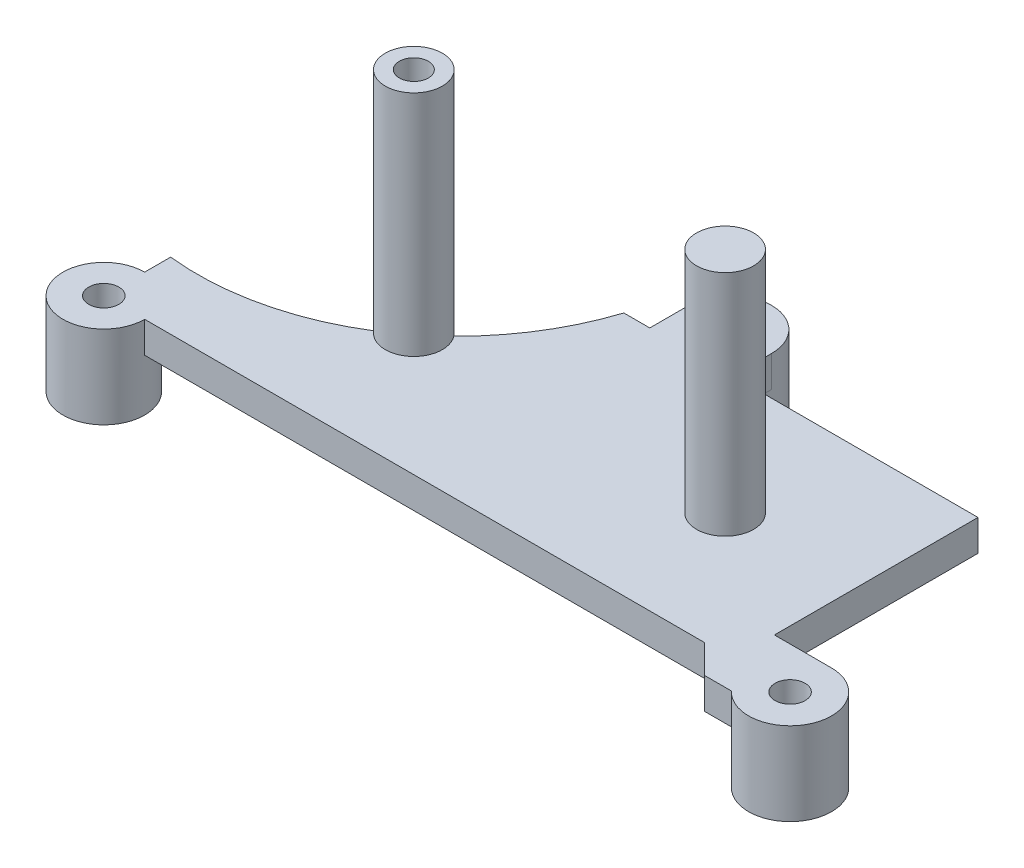
SolidWorks part; units mm, degrees
ref_plane "Front Plane" through (0, 0, 0) normal (0, 0, 1) x (1, 0, 0)
ref_plane "Top Plane" through (0, 0, 0) normal (0, 1, 0) x (1, 0, 0)
ref_plane "Right Plane" through (0, 0, 0) normal (1, 0, 0) x (0, 0, -1)
sketch "Sketch1" plane through (0, 0, 0) normal (0, 1, 0) x (1, 0, 0)
  line L0 (38.5, -3.4862) -> (35.0138, 0)
  line L1 (-38.5, 29.9974) -> (38.5, 29.9974)
  line L2 (-38.5, 29.9974) -> (-38.5, 0)
  line L3 (-38.5, 0) -> (38.5, 0)
  line L4 (38.5, 29.9974) -> (38.5, 0)
  line L5 (-1.6701, 29.9974) -> (8.49, 29.9974)
  line L6 (-1.6701, 29.9974) -> (-1.6701, 34.7599)
  line L7 (-1.6701, 34.7599) -> (8.4899, 34.7599)
  line L8 (8.49, 29.9974) -> (8.4899, 34.7599)
  line L9 (38.5001, 5.08) -> (45.4978, 5.08)
  line L10 (38.5001, 5.08) -> (38.5, -3.4862)
  line L11 (38.5, -3.4862) -> (45.4978, -3.4862)
  line L12 (45.4978, 5.08) -> (45.4978, -3.4862)
  circle A0 centre (-38.5, 0) radius 1.8415
  circle A1 centre (3.4099, 34.7599) radius 1.8415
  circle A2 centre (45.4978, 0) radius 1.8415
  circle A3 centre (-38.5, 0) radius 5.002
  arc A5 (-1.6701, 34.7599) -> (8.4899, 34.7599) centre (3.4099, 34.7599) cw
  circle A6 centre (45.4978, 0) radius 5.08
  dimension "D4" = 3.683
  dimension "D5" = 3.683
  dimension "D3" = 3.683
  dimension "D9" = 10.16
  dimension "D11" = 41.91
  dimension "D1" = 77.0001
  dimension "D2" = 29.9974
  dimension "D6" = 4.7625
  dimension "D7" = 83.9978
  dimension "D8" = 10.16
  dimension "D10" = 6.9977
extrude "Boss-Extrude1" add sketch "Sketch1" along normal blind 3.81 contours A3 L3 L4 L1 L2 | L3 A3 L2 A0 | L2 A3 L3 A0 | L12 A6 L11 A2 | A6 L9 L4 L10 L11 | L11 A6 L12 A2 | A5 L7 A1 | A1 L7 L6 L1 L8 | L10 L3 L0
sketch "Sketch2" plane through (0, 0, 0) normal (0, 1, 0) x (1, 0, 0)
  line L0 (-38.5, 29.9974) -> (-1.6701, 29.9974) construction
  line L2 (-38.5, 29.9974) -> (-38.5, 5.002) construction
  circle A0 centre (-15.5511, 14.9964) radius 7.112
  circle A1 centre (-15.5511, 14.9964) radius 3.4925
  circle A2 centre (22.5489, 14.9964) radius 3.4925
  dimension "D2" = 14.224
  dimension "D3" = 22.9489
  dimension "D4" = 6.985
  dimension "D5" = 6.985
  dimension "D1" = 15.001
  dimension "D6" = 38.1
sketch "Sketch3" plane through (0, 0, 0) normal (0, 1, 0) x (1, 0, 0)
  line L0 (-38.5, 29.9974) -> (-38.5, 5.002) construction
  line L1 (-38.5, 29.9974) -> (-1.6701, 29.9974) construction
  line L2 (-38.5, 8.177) -> (-38.5, 29.9974)
  line L3 (-38.5, 29.9974) -> (-4.8451, 29.9974)
  arc A0 (-38.5, 8.177) -> (-4.8451, 29.9974) centre (-35.0632, 39.7404) ccw
  dimension "D3" = 31.75
  dimension "D1" = 3.175
  dimension "D2" = 3.175
extrude "Cut-Extrude2" cut sketch "Sketch3" along normal blind 3.81 contours L2 A0 L3
extrude "Boss-Extrude2" add sketch "Sketch2" along normal blind 31.75 contours A1 | A2
sketch "Sketch4" plane through (0, 0, 0) normal (0, -1, 0) x (1, 0, 0)
  circle A0 centre (-38.5, 0) radius 5.002
  circle A1 centre (-38.5, 0) radius 1.8415
  circle A2 centre (45.4978, 0) radius 5.08
  circle A3 centre (45.4978, 0) radius 1.8415
  circle A4 centre (3.4099, -34.7599) radius 5.08
  circle A5 centre (3.4099, -34.7599) radius 1.8415
  dimension "D1" = 3.683
  dimension "D2" = 3.683
  dimension "D3" = 3.683
  dimension "D4" = 10.16
extrude "Boss-Extrude3" add sketch "Sketch4" along normal blind 6.35
sketch "Sketch6" plane through (0, 31.75, 0) normal (0, 1, 0) x (1, 0, 0)
  circle A0 centre (-15.5511, 14.9964) radius 1.778
  circle A1 centre (-15.5511, 14.9964) radius 3.4925 construction
  dimension "D1" = 3.556
extrude "Cut-Extrude3" cut sketch "Sketch6" against normal blind 5.08
